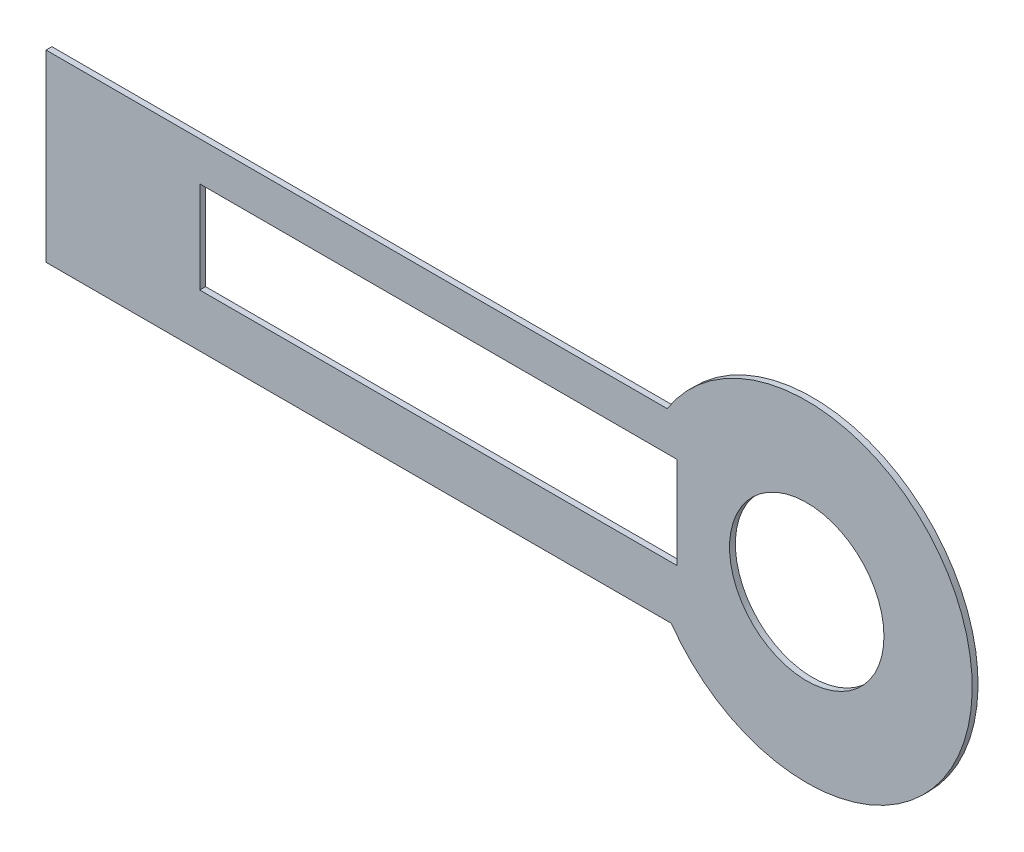
SolidWorks part; units mm, degrees
ref_plane "Front Plane" through (0, 0, 0) normal (0, 0, 1) x (1, 0, 0)
ref_plane "Top Plane" through (0, 0, 0) normal (0, 1, 0) x (1, 0, 0)
ref_plane "Right Plane" through (0, 0, 0) normal (1, 0, 0) x (0, 0, -1)
sketch "Sketch2" plane through (0, 0, 0) normal (0, 0, 1) x (1, 0, 0)
  line L1 (-6.3757, 4.8316) -> (-41.3757, 4.8316)
  line L2 (-6.3757, 4.8316) -> (-6.3757, -5.1684)
  line L3 (-6.3757, -5.1684) -> (-41.3757, -5.1684)
  line L4 (-41.3757, 4.8316) -> (-41.3757, -5.1684)
  circle A0 centre (0, 0) radius 9
  dimension "D1" = 35
  dimension "D3" = 18
  dimension "D2" = 10
extrude "Boss-Extrude2" add sketch "Sketch2" along normal blind 0.3175 contours L1 A0 L3 L2 | L3 A0 L1 L2 | A0 L1 L4 L3
sketch "Sketch3" plane through (0, 0, 0.3175) normal (0, 0, 1) x (1, 0, 0)
  line L1 (-33.0123, 2.708) -> (-7.0557, 2.708)
  line L2 (-33.0123, 2.708) -> (-33.0123, -2.292)
  line L3 (-33.0123, -2.292) -> (-7.0557, -2.292)
  line L4 (-7.0557, 2.708) -> (-7.0557, -2.292)
  circle A0 centre (0, 0) radius 4.2
  dimension "D1" = 5
  dimension "D2" = 8.4
extrude "Cut-Extrude1" cut sketch "Sketch3" against normal through all
